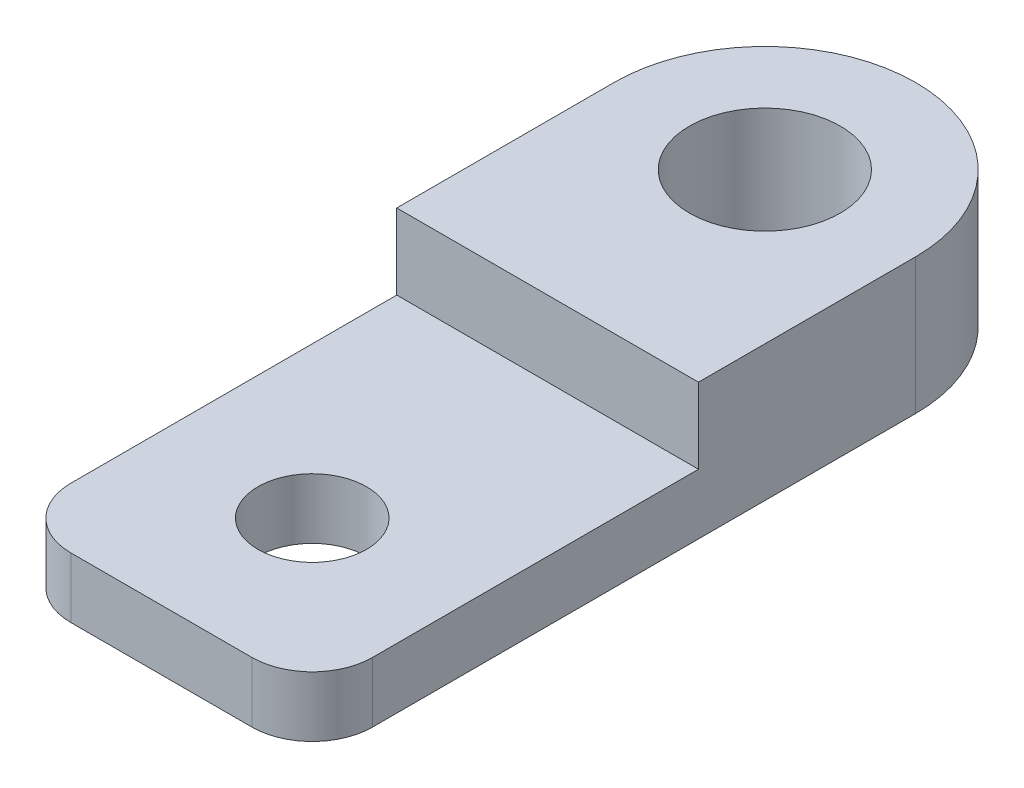
SolidWorks part; units mm, degrees
ref_plane "Front Plane" through (0, 0, 0) normal (0, 0, 1) x (1, 0, 0)
ref_plane "Top Plane" through (0, 0, 0) normal (0, 1, 0) x (1, 0, 0)
ref_plane "Right Plane" through (0, 0, 0) normal (1, 0, 0) x (0, 0, -1)
sketch "Sketch1" plane through (0, 0, 0) normal (0, 1, 0) x (1, 0, 0)
  line L1 (2.54, 0) -> (10.16, 0)
  line L2 (0, 2.54) -> (0, 25.4)
  line L4 (12.7, 2.54) -> (12.7, 25.4)
  arc A0 (12.7, 25.4) -> (0, 25.4) centre (6.35, 25.4) ccw
  circle A1 centre (6.35, 25.4) radius 3.175
  circle A2 centre (6.35, 6.35) radius 2.286
  arc A3 (10.16, 0) -> (12.7, 2.54) centre (10.16, 2.54) ccw
  arc A4 (2.54, 0) -> (0, 2.54) centre (2.54, 2.54) cw
  point P9 (0, 0)
  point P10 (0, 0)
  point P15 (0, 0)
  point P16 (0, 0)
  dimension "D1" = 6.35
  dimension "D2" = 6.35
  dimension "D5" = 4.572
  dimension "D3" = 2.54
  dimension "D4" = 19.05
  dimension "D6" = 6.35
extrude "Boss-Extrude1" add sketch "Sketch1" along normal blind 2.54
sketch "Sketch2" plane through (0, 2.54, 0) normal (0, 1, 0) x (1, 0, 0)
  line L0 (0, 25.4) -> (0, 16.256)
  line L1 (0, 25.4) -> (0, 2.54) construction
  line L2 (0, 16.256) -> (12.7, 16.256)
  line L3 (12.7, 2.54) -> (12.7, 25.4) construction
  line L4 (12.7, 16.256) -> (12.7, 25.4)
  circle A0 centre (6.35, 25.4) radius 3.175 construction
  arc A1 (12.7, 25.4) -> (0, 25.4) centre (6.35, 25.4) ccw construction
  circle A2 centre (6.35, 25.4) radius 3.175
  arc A3 (12.7, 25.4) -> (0, 25.4) centre (6.35, 25.4) ccw
  dimension "D1" = 9.144
extrude "Boss-Extrude2" add sketch "Sketch2" along normal blind 3.175
